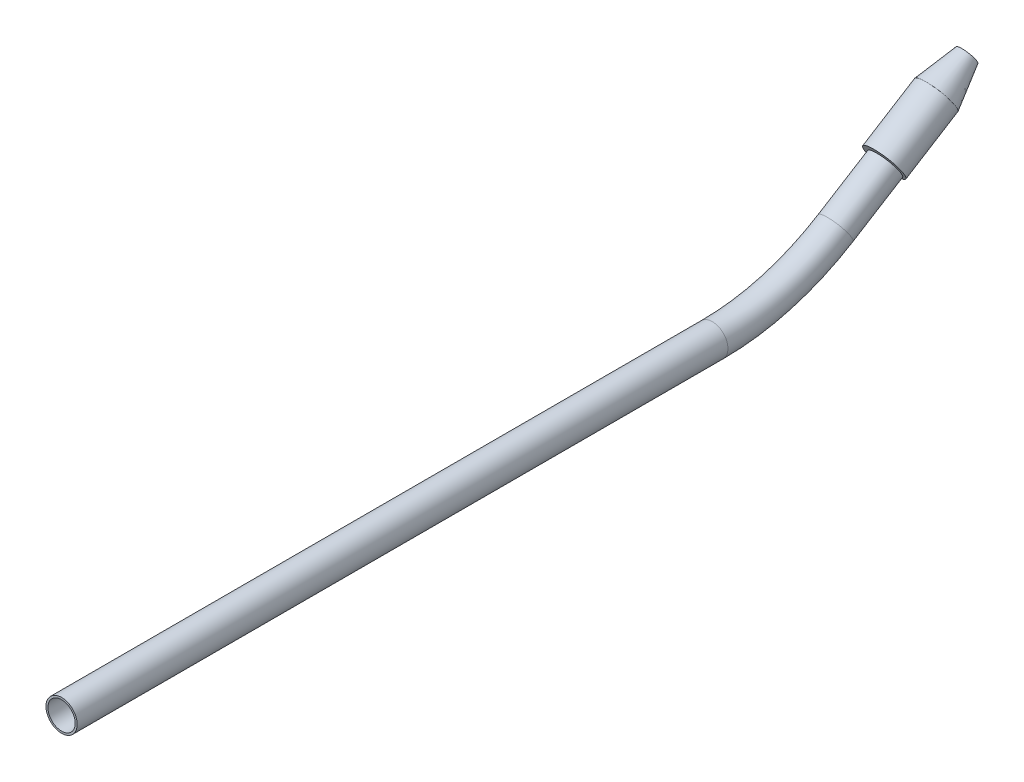
SolidWorks part; units mm, degrees
material "Plain Carbon Steel"
ref_plane "Спереди" through (0, 0, 0) normal (0, 0, 1) x (1, 0, 0)
ref_plane "Сверху" through (0, 0, 0) normal (0, 1, 0) x (1, 0, 0)
ref_plane "Справа" through (0, 0, 0) normal (1, 0, 0) x (0, 0, -1)
other "Configuration Table"
sketch "Sketch1" plane through (0, 0, 0) normal (1, 0, 0) x (0, 0, -1)
  line L0 (-7.8293, 0) -> (75.6736, 0)
  line L3 (97.8446, 8.4511) -> (91.4913, 4.5088)
  arc A0 (91.4913, 4.5088) -> (75.6736, 0) centre (75.6736, 30) cw
  dimension "D1" = 30
sketch "Sketch2" plane through (0, 0, 0) normal (0, 0, 1) x (1, 0, 0)
  circle A0 centre (0, 0) radius 2
  circle A1 centre (0, 0) radius 1.75
sweep "Sweep1" add profiles "Sketch2" path "Sketch1"
sketch "Sketch3" plane through (0, 0, 0) normal (1, 0, 0) x (0, 0, -1)
  line L0 (-7.8293, -57.121) -> (108.3454, 15.2803) construction
  line L1 (-7.8293, -55.0615) -> (-7.8293, -59.1806) construction
  line L2 (98.0634, 8.136) -> (99.0422, 6.5654)
  line L3 (99.0422, 6.5654) -> (105.7173, 10.7254)
  line L4 (109.0054, 14.219) -> (108.6749, 14.7492)
  line L5 (105.7173, 10.7254) -> (109.0054, 14.219)
  line L6 (108.6749, 14.7492) -> (98.0634, 8.136)
revolve "Revolve1" add sketch "Sketch3" angle 360 about L0
